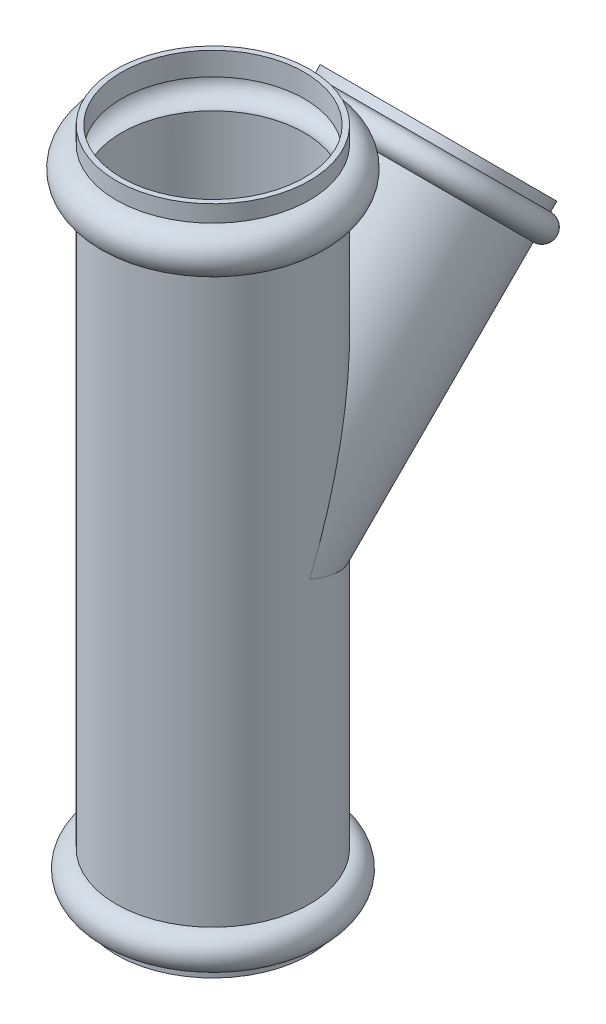
SolidWorks part; units mm, degrees
ref_plane "Спереди" through (0, 0, 0) normal (0, 0, 1) x (1, 0, 0)
ref_plane "Сверху" through (0, 0, 0) normal (0, 1, 0) x (1, 0, 0)
ref_plane "Справа" through (0, 0, 0) normal (1, 0, 0) x (0, 0, -1)
sketch "Эскиз2" plane through (0, 0, 0) normal (0, 0, 1) x (1, 0, 0)
  line L0 (55, 163.1018) -> (55, -160)
  line L1 (55, 186.8982) -> (55, 196.4492)
  line L2 (55, -180) -> (55, -185)
  line L3 (0, 137.8137) -> (0, -119.9955) construction
  arc A0 (55, 163.1018) -> (55, 186.8982) centre (55, 175) ccw
  arc A1 (55, -160) -> (55, -180) centre (55, -170) cw
revolve "Повернуть-Тонкостенный1" add sketch "Эскиз2" angle 360 about L3
ref_plane "Плоскость1" through (0, 0, 0) normal (0, 0.7071, 0.7071) x (-1, 0, 0)
sketch "Эскиз3" plane through (0, 0, 0) normal (0, 0.7071, 0.7071) x (1, 0, 0)
  line L0 (55, 162.5147) -> (55, 0)
  line L1 (0, 125.3985) -> (0, 59.7564) construction
  line L2 (55, 181.5147) -> (55, 176.5147)
  arc A0 (55, 176.5147) -> (55, 162.5147) centre (55, 169.5147) cw
revolve "Повернуть-Тонкостенный3" add sketch "Эскиз3" angle 360 about L1
